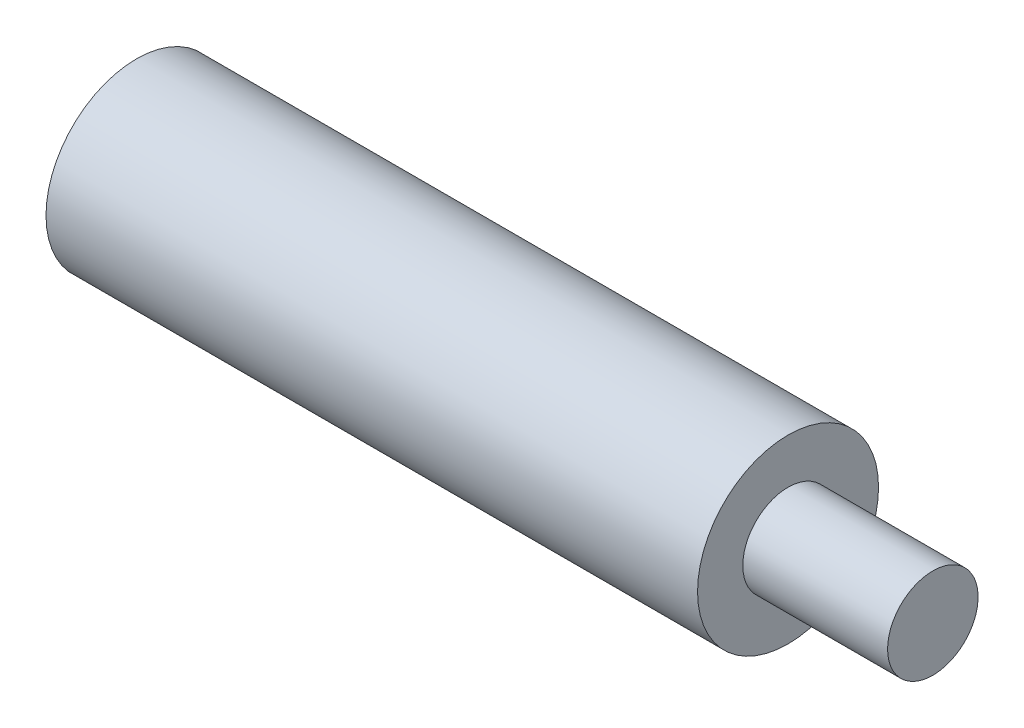
SolidWorks part; units mm, degrees
material "Messing"
ref_plane "Ebene vorne" through (0, 0, 0) normal (0, 0, 1) x (1, 0, 0)
ref_plane "Ebene oben" through (0, 0, 0) normal (0, 1, 0) x (1, 0, 0)
ref_plane "Ebene rechts" through (0, 0, 0) normal (1, 0, 0) x (0, 0, -1)
sketch "Skizze1" plane through (0, 0, 0) normal (0, 0, 1) x (1, 0, 0)
  line L0 (0, 0) -> (44, 0) construction
  line L1 (0, 0) -> (0, 5)
  line L2 (0, 5) -> (36, 5)
  line L3 (36, 5) -> (36, 2.5)
  line L4 (36, 2.5) -> (44, 2.5)
  line L5 (44, 2.5) -> (44, 0)
  line L6 (0, 0) -> (44, 0)
  line L7 (0, 0) -> (20.0134, 0) construction
  dimension "D1" = 10
  dimension "D2" = 8
  dimension "D3" = 5
  dimension "D4" = 36
revolve "Rotation1" add sketch "Skizze1" angle 360 about L0
hole_wizard "M5 Gewindebohrung1" positions "Skizze2" profile "Skizze3" tap size "M5" standard "DIN"
sketch "Skizze2" plane through (0, 0, 0) normal (-1, 0, 0) x (0, 0, 1)
  point P0 (0, 0)
sketch "Skizze3" plane through (0, 0, 0) normal (0, 1, 0) x (0, 0, 1)
  line L0 (0, 0) -> (0, 15.2618)
  line L1 (0, 15.2618) -> (2.1, 14)
  line L2 (2.1, 14) -> (2.1, 0)
  line L5 (2.1, 0) -> (0, 0)
  line L10 (0, 15.2618) -> (-2.1, 14) construction
  line L11 (0, -6.35) -> (0, 107.95) construction
  dimension "Bohrerdurchmesser" = 4.2
  dimension "Bohrungstiefe" = 14
  dimension "Spitzenwinkel" = 118
cosmetic thread "Bohrungsgewinde1" parameters "D1"=10, "D2"=5
